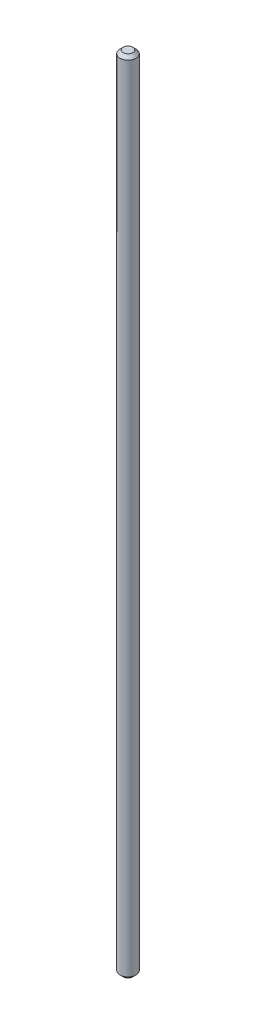
SolidWorks part; units mm, degrees
ref_plane "Plan de face" through (0, 0, 0) normal (0, 0, 1) x (1, 0, 0)
ref_plane "Plan de dessus" through (0, 0, 0) normal (0, 1, 0) x (1, 0, 0)
ref_plane "Plan de droite" through (0, 0, 0) normal (1, 0, 0) x (0, 0, -1)
sketch "Esquisse1" plane through (0, 0, 0) normal (0, 1, 0) x (1, 0, 0)
  circle A0 centre (0, 0) radius 2.5
  dimension "D1" = 5
extrude "Boss.-Extru.1" add sketch "Esquisse1" along normal blind 250
chamfer "Chanfrein1" distance 1 angle 45 2 edges at (0, 0, 2.5) (0, 250, 2.5)
